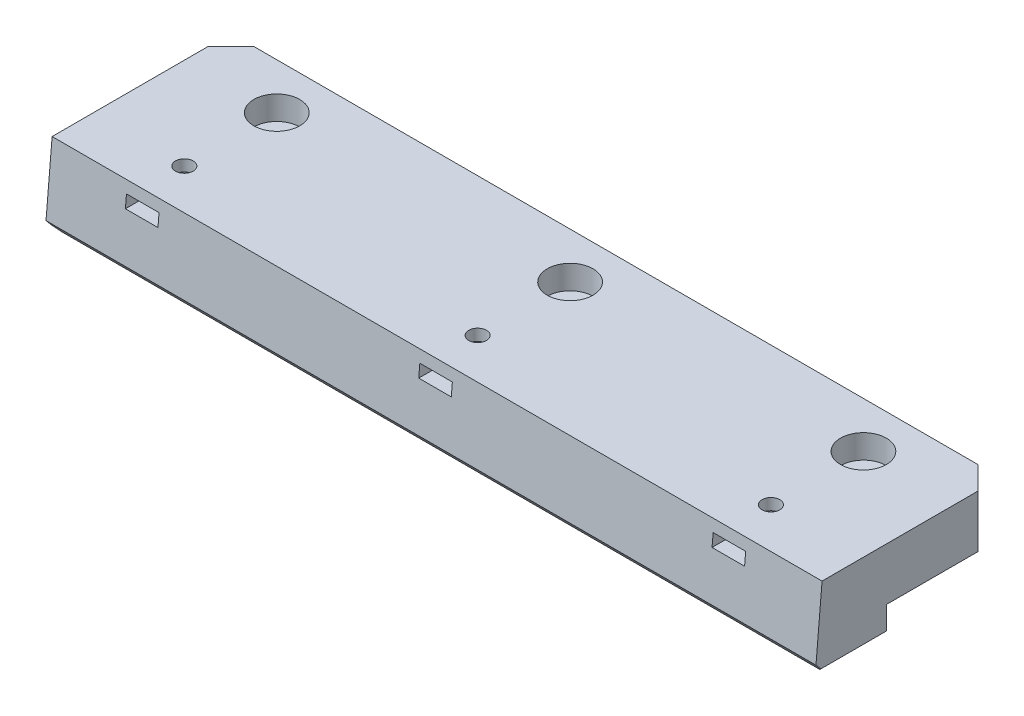
SolidWorks part; units mm, degrees
material "PET"
ref_plane "Front Plane" through (0, 0, 0) normal (0, 0, 1) x (1, 0, 0)
ref_plane "Top Plane" through (0, 0, 0) normal (0, 1, 0) x (1, 0, 0)
ref_plane "Right Plane" through (0, 0, 0) normal (1, 0, 0) x (0, 0, -1)
sketch "Sketch1" plane through (0, 0, 0) normal (1, 0, 0) x (0, 0, -1)
  line L1 (12.7, -4.7625) -> (-12.7, -4.7625)
  line L2 (12.7, -4.7625) -> (12.7, 4.7625)
  line L3 (12.7, 4.7625) -> (-12.7, 4.7625)
  line L4 (-12.7, -4.7625) -> (-12.7, 4.7625)
  line L5 (12.7, -4.7625) -> (-12.7, 4.7625) construction
  line L6 (12.7, 4.7625) -> (-12.7, -4.7625) construction
  point P0 (0, 0)
  dimension "D1" = 9.525
  dimension "D2" = 25.4
extrude "Boss-Extrude1" add sketch "Sketch1" along normal mid plane 213.36
sketch "Sketch2" plane through (-106.68, 0, 0) normal (-1, 0, 0) x (0, 0, 1)
  line L0 (12.7, 4.7625) -> (37.438, 4.7625)
  line L1 (12.7, 4.7625) -> (12.7, -4.7625) construction
  line L2 (37.438, 4.7625) -> (38.829, -11.1363)
  line L4 (38.829, -11.1363) -> (12.7, -11.1363)
  line L9 (12.7, -11.1363) -> (12.7, 4.7625)
  line L10 (-12.7, 4.7625) -> (12.7, 4.7625) construction
  line L11 (25.5674, 149.1875) -> (39.494, -9.9944) construction
  line L12 (19.05, -11.1363) -> (38.1, -11.1363) construction
  dimension "D1" = 0.762
extrude "Boss-Extrude2" add sketch "Sketch2" against normal through all
chamfer "Chamfer1" distance 6.35 angle 45 4 edges at (106.68, -7.9494, 12.7) (-106.68, 0, -12.7) (106.68, 0, -12.7) (-106.68, -7.9494, 12.7)
chamfer "Chamfer2" distance 3.175 angle 45 1 edges at (0, -11.1363, 38.829)
hole_wizard "#8 Clearance Hole1" positions "Sketch3" profile "Sketch4" hole size "#8" standard "ANSI Inch" end condition up to next
sketch "Sketch3" plane through (0, -11.1363, 0) normal (0, -1, 0) x (-1, 0, 0)
  line L0 (0, -38.5523) -> (0, -12.7) construction
  line L1 (106.68, -38.5523) -> (-106.68, -38.5523) construction
  line L2 (-100.33, -12.7) -> (100.33, -12.7) construction
  line L3 (0, -12.7) -> (0, 12.7) construction
  line L4 (-100.33, 12.7) -> (100.33, 12.7) construction
  line L6 (0, 0) -> (106.68, 0) construction
  line L7 (106.68, -19.05) -> (106.68, 6.35) construction
  line L9 (0, -25.6261) -> (106.68, -25.6261) construction
  line L10 (106.68, -19.05) -> (106.68, -35.8983) construction
  point P12 (0, 0)
  point P19 (0, -25.6261)
  point P24 (81.28, -25.6261)
  point P26 (81.28, 0)
  point P35 (-81.28, 0)
  point P36 (-81.28, -25.6261)
  dimension "D1" = 25.4
sketch "Sketch4" plane through (81.28, -11.1363, 25.6261) normal (1, 0, 0) x (0, 0, -1)
  line L0 (0, 0) -> (0, 15.8988)
  line L1 (0, 15.8988) -> (2.4574, 15.8988)
  line L2 (2.4574, 15.8988) -> (2.4574, 0)
  line L5 (2.4574, 0) -> (0, 0)
  line L11 (0, -6.35) -> (0, 107.95) construction
  dimension "Thru Hole Dia." = 4.9149
  dimension "Thru Hole Depth" = 15.8988
chamfer "Chamfer3" distance 1.5875 angle 45 10 edges at (-106.68, -4.7625, 6.35) (-103.505, -4.7625, -9.525) (0, -4.7625, -12.7) (103.505, -4.7625, -9.525) (106.68, -4.7625, 6.35) (106.68, -11.1363, 27.4741) (103.505, -11.1363, 15.875) (0, -11.1363, 12.7) (-103.505, -11.1363, 15.875) (-106.68, -11.1363, 27.4741)
sketch "Sketch5" plane through (0, 4.7625, 0) normal (0, 1, 0) x (1, 0, 0)
  line L0 (106.68, 6.35) -> (106.68, -37.438) construction
  line L1 (85.7885, -37.438) -> (85.7885, -23.0232)
  line L2 (85.7885, -23.0232) -> (81.28, -20.4202)
  line L3 (81.28, -20.4202) -> (76.7715, -23.0232)
  line L4 (76.7715, -23.0232) -> (76.7715, -37.438)
  line L20 (73.5965, -37.438) -> (76.7715, -37.438)
  line L21 (73.5965, -37.438) -> (73.5965, -17.2452)
  line L22 (73.5965, -17.2452) -> (88.9635, -17.2452)
  line L23 (88.9635, -37.438) -> (88.9635, -17.2452)
  line L24 (76.7715, -28.2291) -> (81.28, -30.8321) [skipped]
  line L25 (81.28, -30.8321) -> (85.7885, -28.2291) [skipped]
  line L26 (85.7885, -37.438) -> (88.9635, -37.438)
  line L27 (81.28, -20.4202) -> (81.28, -17.2452) construction
  line L28 (4.5085, -37.438) -> (4.5085, -23.0232)
  line L29 (4.5085, -23.0232) -> (0, -20.4202)
  line L30 (0, -20.4202) -> (-4.5085, -23.0232)
  line L31 (-4.5085, -23.0232) -> (-4.5085, -37.438)
  line L32 (-7.6835, -37.438) -> (-4.5085, -37.438)
  line L33 (-7.6835, -37.438) -> (-7.6835, -17.2452)
  line L34 (-7.6835, -17.2452) -> (7.6835, -17.2452)
  line L35 (7.6835, -37.438) -> (7.6835, -17.2452)
  line L36 (4.5085, -37.438) -> (7.6835, -37.438)
  line L37 (0, -20.4202) -> (0, -17.2452) construction
  line L38 (-76.7715, -37.438) -> (-76.7715, -23.0232)
  line L39 (-76.7715, -23.0232) -> (-81.28, -20.4202)
  line L40 (-81.28, -20.4202) -> (-85.7885, -23.0232)
  line L41 (-85.7885, -23.0232) -> (-85.7885, -37.438)
  line L42 (-88.9635, -37.438) -> (-85.7885, -37.438)
  line L43 (-88.9635, -37.438) -> (-88.9635, -17.2452)
  line L44 (-88.9635, -17.2452) -> (-73.5965, -17.2452)
  line L45 (-73.5965, -37.438) -> (-73.5965, -17.2452)
  line L46 (-76.7715, -37.438) -> (-73.5965, -37.438)
  line L47 (-81.28, -20.4202) -> (-81.28, -17.2452) construction
  line L48 (85.7885, -37.438) -> (4.5085, -37.438) construction
  line L49 (106.68, -37.438) -> (-106.68, -37.438) construction
  circle A0 centre (81.28, -25.6261) radius 4.5085 construction
  circle A1 centre (0, -25.6261) radius 4.5085 construction
  circle A2 centre (-81.28, -25.6261) radius 4.5085 construction
  dimension "D1" = 9.017
  dimension "D2" = 3.175
  dimension "D3" = 3
  dimension "D4" = 81.28
  dimension "D5" = 0
extrude "Boss-Extrude3" add sketch "Sketch5" along normal blind 3.429
sketch "Sketch6" plane through (0, 8.1915, 0) normal (0, 1, 0) x (1, 0, 0)
  line L1 (-88.9635, -17.2452) -> (-73.5965, -17.2452)
  line L2 (-88.9635, -17.2452) -> (-88.9635, -37.438)
  line L3 (-88.9635, -37.438) -> (-73.5965, -37.438)
  line L4 (-73.5965, -17.2452) -> (-73.5965, -37.438)
  line L5 (-7.6835, -17.2452) -> (7.6835, -17.2452)
  line L6 (-7.6835, -17.2452) -> (-7.6835, -37.438)
  line L7 (-7.6835, -37.438) -> (7.6835, -37.438)
  line L8 (7.6835, -17.2452) -> (7.6835, -37.438)
  line L9 (73.5965, -17.2452) -> (88.9635, -17.2452)
  line L10 (73.5965, -17.2452) -> (73.5965, -37.438)
  line L11 (73.5965, -37.438) -> (88.9635, -37.438)
  line L12 (88.9635, -17.2452) -> (88.9635, -37.438)
  circle A0 centre (81.28, -25.6261) radius 2.4574 construction
  circle A1 centre (0, -25.6261) radius 2.4574 construction
  circle A2 centre (-81.28, -25.6261) radius 2.4574 construction
  circle A3 centre (81.28, -25.6261) radius 2.4574
  circle A4 centre (0, -25.6261) radius 2.4574
  circle A5 centre (-81.28, -25.6261) radius 2.4574
extrude "Boss-Extrude4" add sketch "Sketch6" along normal blind 3.175
chamfer "Chamfer4" [suppressed] distance 6.604 angle 45
sketch "Sketch7" plane through (0, 4.7625, 0) normal (0, 1, 0) x (1, 0, 0)
  line L44 (-73.5965, -17.2452) -> (-73.5965, -37.438)
  line L45 (-73.5965, -37.438) -> (-7.6835, -37.438)
  line L47 (-7.6835, -37.438) -> (-7.6835, -17.2452)
  line L49 (-7.6835, -17.2452) -> (7.6835, -17.2452)
  line L50 (7.6835, -17.2452) -> (7.6835, -37.438)
  line L51 (7.6835, -37.438) -> (73.5965, -37.438)
  line L52 (73.5965, -37.438) -> (73.5965, -17.2452)
  line L53 (73.5965, -17.2452) -> (88.9635, -17.2452)
  line L54 (88.9635, -17.2452) -> (88.9635, -37.438)
  line L55 (88.9635, -37.438) -> (106.68, -37.438)
  line L56 (106.68, -37.438) -> (106.68, 6.35)
  line L57 (106.68, 6.35) -> (100.33, 12.7)
  line L58 (100.33, 12.7) -> (-100.33, 12.7)
  line L59 (-100.33, 12.7) -> (-106.68, 6.35)
  line L60 (-106.68, 6.35) -> (-106.68, -37.438)
  line L61 (-106.68, -37.438) -> (-88.9635, -37.438)
  line L62 (-88.9635, -37.438) -> (-88.9635, -17.2452)
  line L63 (-88.9635, -17.2452) -> (-73.5965, -17.2452)
  line L64 (-73.5965, -17.2452) -> (-73.5965, -37.438)
  line L65 (-73.5965, -37.438) -> (-7.6835, -37.438)
  line L66 (-7.6835, -37.438) -> (-7.6835, -17.2452)
  line L67 (-7.6835, -17.2452) -> (7.6835, -17.2452)
  line L68 (7.6835, -17.2452) -> (7.6835, -37.438)
  line L69 (7.6835, -37.438) -> (73.5965, -37.438)
  line L70 (73.5965, -37.438) -> (73.5965, -17.2452)
  line L71 (73.5965, -17.2452) -> (88.9635, -17.2452)
  line L72 (88.9635, -17.2452) -> (88.9635, -37.438)
  line L73 (88.9635, -37.438) -> (106.68, -37.438)
  line L74 (106.68, -37.438) -> (106.68, 6.35)
  line L75 (106.68, 6.35) -> (100.33, 12.7)
  line L76 (100.33, 12.7) -> (-100.33, 12.7)
  line L77 (-100.33, 12.7) -> (-106.68, 6.35)
  line L78 (-106.68, 6.35) -> (-106.68, -37.438)
  line L79 (-106.68, -37.438) -> (-88.9635, -37.438)
  line L80 (-88.9635, -37.438) -> (-88.9635, -17.2452)
  line L81 (-88.9635, -17.2452) -> (-73.5965, -17.2452)
  circle A0 centre (81.28, 0) radius 6.35
  circle A1 centre (0, 0) radius 6.35
  circle A2 centre (-81.28, 0) radius 6.35
  dimension "D5" = 12.7
  dimension "D1" = 0
extrude "Boss-Extrude5" add sketch "Sketch7" along normal up to surface (6.604 mm away) up to face at (81.28, 11.3665, 27.3416)
sketch "Sketch8" plane through (-106.68, 0, 0) normal (-1, 0, 0) x (0, 0, 1)
  line L0 (37.438, 4.7625) -> (36.8603, 11.3665)
  line L2 (36.8603, 11.3665) -> (37.438, 11.3665)
  line L3 (37.438, 11.3665) -> (37.438, 4.7625)
  line L4 (38.5523, -7.9734) -> (37.438, 4.7625) construction
  line L5 (-6.35, 11.3665) -> (37.438, 11.3665) construction
extrude "Cut-Extrude1" cut sketch "Sketch8" against normal through all
